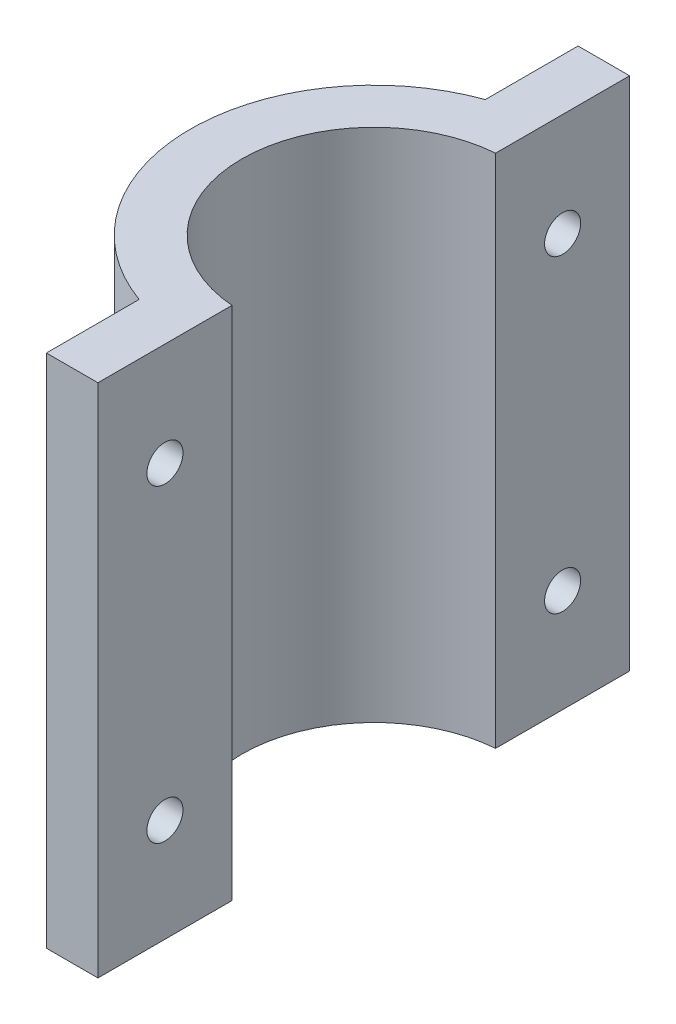
SolidWorks part; units mm, degrees
ref_plane "Front Plane" through (0, 0, 0) normal (0, 0, 1) x (1, 0, 0)
ref_plane "Top Plane" through (0, 0, 0) normal (0, 1, 0) x (1, 0, 0)
ref_plane "Right Plane" through (0, 0, 0) normal (1, 0, 0) x (0, 0, -1)
sketch "Sketch6" plane through (0, 0, 0) normal (0, -1, 0) x (1, 0, 0)
  line L5 (-1, 25.7848) -> (-1, 12.786)
  line L6 (-1, 25.7848) -> (-6, 25.7848)
  line L7 (-6, 25.7848) -> (-6, 16.7848)
  line L8 (-6, -16.7848) -> (-6, -25.7848)
  line L9 (-6, -25.7848) -> (-1, -25.7848)
  line L10 (-1, -25.7848) -> (-1, -12.786)
  line L11 (-12.825, 0) -> (-17.825, 0) construction
  arc A0 (-1, 12.786) -> (-1, -12.786) centre (0, 0) ccw
  arc A1 (-6, 16.7848) -> (-6, -16.7848) centre (0, 0) ccw
  dimension "D1" = 25.65
  dimension "D2" = 5
  dimension "D3" = 1
  dimension "D4" = 9
extrude "Boss-Extrude4" add sketch "Sketch6" along normal blind 50
sketch "Sketch7" plane through (-1, 0, 0) normal (1, 0, 0) x (0, 0, -1)
  line L0 (-19.2854, -50) -> (-19.2854, 0) construction
  line L3 (0, 0) -> (0, -50) construction
  line L6 (-25.7848, -25) -> (25.7848, -25) construction
  line L11 (-12.786, 0) -> (-25.7848, 0) construction
  line L12 (-12.786, -50) -> (-25.7848, -50) construction
  line L13 (-25.7848, -50) -> (-25.7848, 0) construction
  line L14 (25.7848, -50) -> (25.7848, 0) construction
  line L15 (-12.786, -50) -> (12.786, -50) construction
  circle A0 centre (-19.2854, -10) radius 1.75
  circle A1 centre (-19.2854, -40) radius 1.75
  circle A2 centre (19.2854, -40) radius 1.75
  circle A3 centre (19.2854, -10) radius 1.75
  dimension "D1" = 10
  dimension "D2" = 3.5
extrude "Cut-Extrude1" cut sketch "Sketch7" against normal through all
